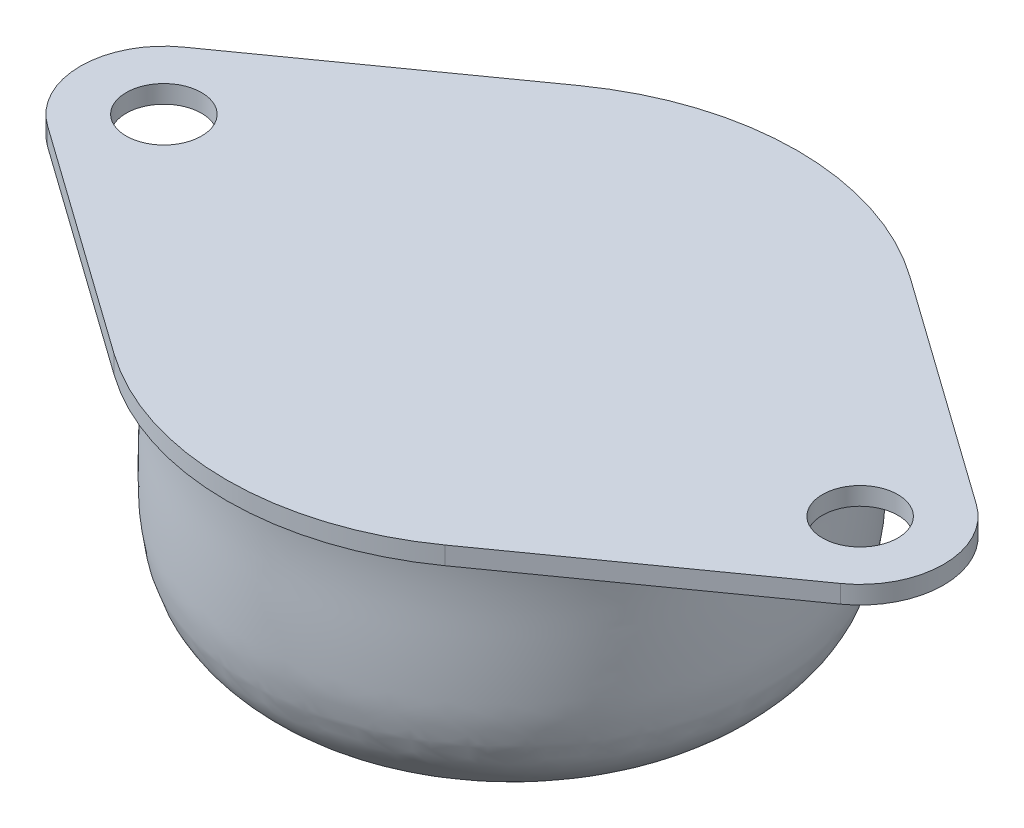
SolidWorks part; units mm, degrees
ref_plane "前视基准面" through (0, 0, 0) normal (0, 0, 1) x (1, 0, 0)
ref_plane "上视基准面" through (0, 0, 0) normal (0, 1, 0) x (1, 0, 0)
ref_plane "右视基准面" through (0, 0, 0) normal (1, 0, 0) x (0, 0, -1)
sketch "草图1" plane through (0, 0, 0) normal (0, 0, 1) x (1, 0, 0)
  line L0 (103.6877, 299.2167) -> (755.5909, 299.2167) construction
  line L1 (0, 0) -> (0, -3.2981) construction
  line L2 (14.9446, 15.7019) -> (0, 15.7019)
  line L3 (0, -3.2981) -> (0, 15.7019)
  spline S0 degree 3 poles (0, -3.2981) (0.7065, -3.3326) (1.6911, -3.2191) (2.7732, -2.87) (3.305, -2.6653) (3.6824, -2.517) (4.0506, -2.3552) (4.4167, -2.2048) (4.7782, -2.0037) (5.0999, -1.7545) (5.4692, -1.5501) (5.8618, -1.2451) (6.265, -0.9233) (6.631, -0.5441) (6.9249, -0.14) (7.3706, 0.0487) (7.7722, 0.1611) (8.159, 0.2479) (8.5784, 0.3585) (9.1095, 0.547) (9.6982, 0.7207) (10.2598, 0.911) (10.7476, 1.0281) (11.1603, 1.2148) (11.5648, 1.4812) (12.0002, 1.6804) (12.4563, 1.9789) (12.8877, 2.3398) (13.2914, 2.7704) (13.6221, 3.1716) (13.8755, 3.5742) (14.1046, 3.9831) (14.2481, 4.5081) (14.4533, 4.978) (14.5533, 5.6135) (14.6888, 6.3529) (14.7446, 7.8503) (14.7397, 9.9174) (14.6107, 12.7254) (14.7456, 14.6551) (14.9446, 15.7019) knots 0 0 0 0 0.07498 0.104145 0.120683 0.135565 0.147239 0.163439 0.177615 0.191043 0.206611 0.222342 0.243823 0.261329 0.27846 0.295788 0.311179 0.323053 0.337864 0.357273 0.382918 0.403098 0.420289 0.436132 0.450934 0.471702 0.486864 0.508751 0.531303 0.549552 0.563885 0.581875 0.599061 0.621526 0.636019 0.667207 0.701413 0.794955 0.887064 1 1 1 1
  dimension "D1" = 19
revolve "旋转1" add sketch "草图1" angle 360 about L3
sketch "草图2" plane through (0, 15.7019, 0) normal (0, 1, 0) x (1, 0, 0)
  line L0 (0, 0) -> (0, 11.1104) construction
  line L1 (9.2204, 12.9536) -> (22.0965, 3.7883)
  line L2 (22.0965, -3.7883) -> (9.2204, -12.9536)
  line L3 (-22.0965, -3.7883) -> (-9.2204, -12.9536)
  line L4 (-9.2204, 12.9536) -> (-22.0965, 3.7883)
  arc A0 (9.2204, 12.9536) -> (-9.2204, 12.9536) centre (0, 0) ccw
  circle A1 centre (19.4, 0) radius 2.1
  arc A2 (22.0965, -3.7883) -> (22.0965, 3.7883) centre (19.4, 0) ccw
  arc A3 (-22.0965, -3.7883) -> (-22.0965, 3.7883) centre (-19.4, 0) cw
  circle A4 centre (-19.4, 0) radius 2.1
  arc A5 (-9.2204, -12.9536) -> (9.2204, -12.9536) centre (0, 0) ccw
  dimension "D1" = 31.8
  dimension "D2" = 4.2
  dimension "D4" = 9.3
  dimension "D3" = 38.8
extrude "凸台-拉伸1" add sketch "草图2" against normal blind 1
